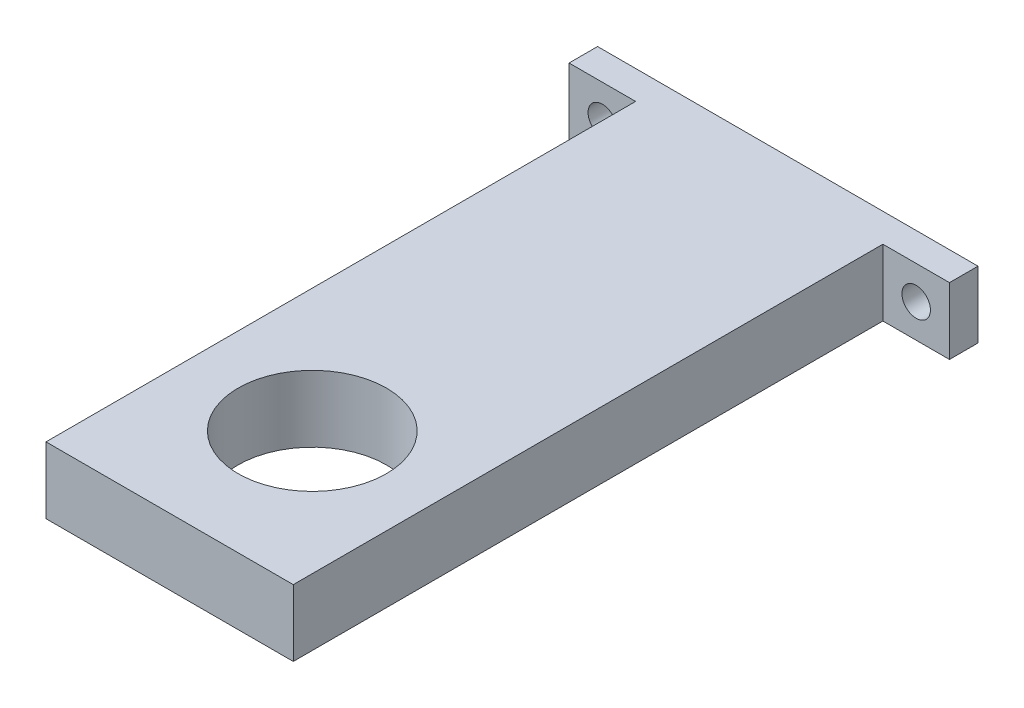
SolidWorks part; units mm, degrees
ref_plane "Front" through (0, 0, 0) normal (0, 0, 1) x (1, 0, 0)
ref_plane "Top" through (0, 0, 0) normal (0, 1, 0) x (1, 0, 0)
ref_plane "Right" through (0, 0, 0) normal (1, 0, 0) x (0, 0, -1)
sketch "Эскиз1" plane through (0, 0, 0) normal (0, 0, 1) x (1, 0, 0)
  line L1 (-20, 3.5) -> (20, 3.5)
  line L2 (-20, 3.5) -> (-20, -3.5)
  line L3 (-20, -3.5) -> (20, -3.5)
  line L4 (20, 3.5) -> (20, -3.5)
  line L5 (-20, 3.5) -> (20, -3.5) construction
  line L6 (-20, -3.5) -> (20, 3.5) construction
  point P0 (0, 0)
  dimension "D1" = 7
  dimension "D2" = 40
extrude "Бобышка-Вытянуть1" add sketch "Эскиз1" along normal blind 3
sketch "Эскиз2" plane through (0, 0, 3) normal (0, 0, 1) x (1, 0, 0)
  line L0 (20, 3.5) -> (-20, 3.5) construction
  line L1 (-13, 3.5) -> (13, 3.5)
  line L2 (-13, 3.5) -> (-13, -3.5)
  line L3 (-13, -3.5) -> (13, -3.5)
  line L4 (13, 3.5) -> (13, -3.5)
  line L5 (-20, -3.5) -> (20, -3.5) construction
  line L6 (-20, 3.5) -> (-20, -3.5) construction
  line L7 (20, -3.5) -> (20, 3.5) construction
  dimension "D1" = 7
  dimension "D2" = 7
extrude "Бобышка-Вытянуть2" add sketch "Эскиз2" along normal blind 62
sketch "Эскиз3" plane through (0, -3.5, 0) normal (0, -1, 0) x (-1, 0, 0)
  line L0 (20, 0) -> (-20, 0) construction
  line L1 (13, -65) -> (13, -3) construction
  circle A0 centre (0, -50) radius 7.8
  dimension "D2" = 15.6
  dimension "D1" = 50
  dimension "D3" = 13
extrude "Вырез-Вытянуть1" cut sketch "Эскиз3" against normal blind 7
sketch "Эскиз4" plane through (0, 0, 3) normal (0, 0, 1) x (1, 0, 0)
  line L0 (-20, 3.5) -> (-20, -3.5) construction
  line L1 (-13, 3.5) -> (-20, 3.5) construction
  circle A0 centre (-16.5, 0) radius 1.5
  dimension "D3" = 3
  dimension "D1" = 3.5
  dimension "D2" = 3.5
extrude "Вырез-Вытянуть2" cut sketch "Эскиз4" against normal blind 7
sketch "Эскиз5" plane through (0, 0, 3) normal (0, 0, 1) x (1, 0, 0)
  line L0 (20, 3.5) -> (13, 3.5) construction
  line L1 (20, -3.5) -> (20, 3.5) construction
  circle A0 centre (16.5, 0) radius 1.5
  dimension "D1" = 3
  dimension "D2" = 3.5
  dimension "D3" = 3.5
extrude "Вырез-Вытянуть3" cut sketch "Эскиз5" against normal blind 7
